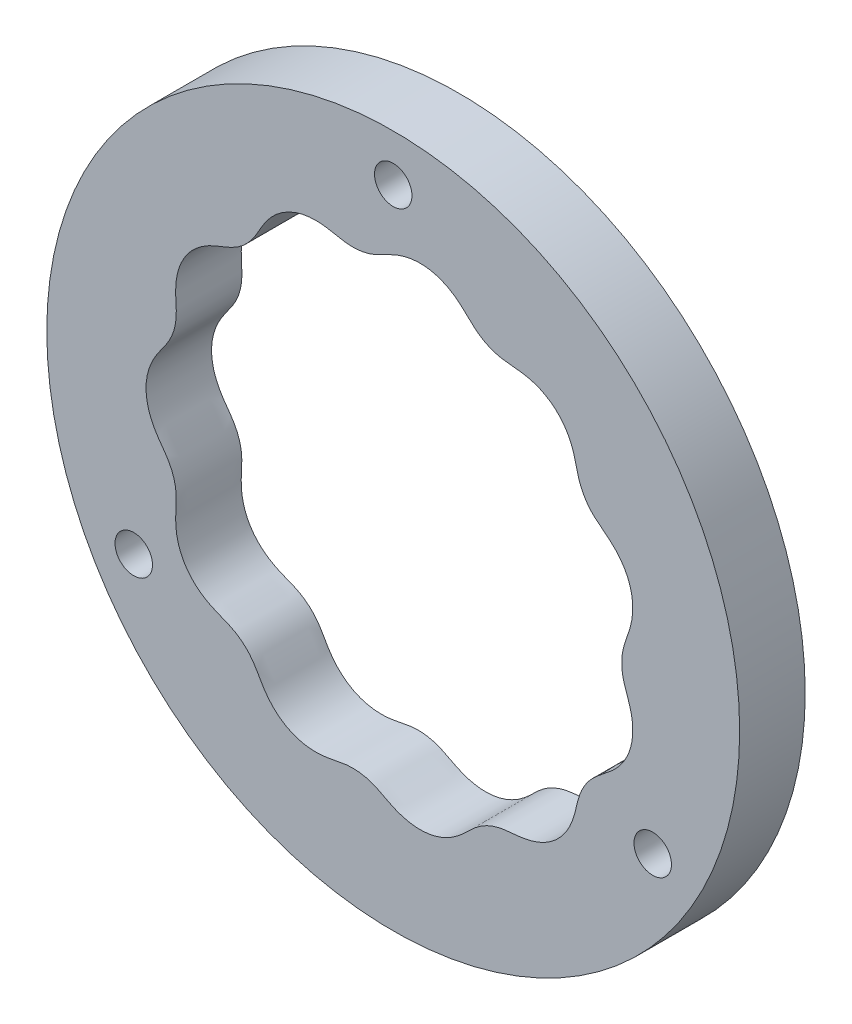
SolidWorks part; units mm, degrees
ref_plane "Front Plane" through (0, 0, 0) normal (0, 0, 1) x (1, 0, 0)
ref_plane "Top Plane" through (0, 0, 0) normal (0, 1, 0) x (1, 0, 0)
ref_plane "Right Plane" through (0, 0, 0) normal (1, 0, 0) x (0, 0, -1)
curve "Curve1"
sketch "Sketch2" plane through (0, 0, 0) normal (0, 0, 1) x (1, 0, 0)
  circle A0 centre (0, 0) radius 37
  dimension "D1" = 74
extrude "Boss-Extrude1" add sketch "Sketch2" along normal blind 7
sketch "Sketch3" plane through (0, 0, 0) normal (0, 0, 1) x (1, 0, 0)
  spline S3 degree 3 poles (-23.4157, -6.8604) (-23.2888, -7.2958) (-23.217, -7.7095) (-23.1554, -8.5437) (-23.1678, -8.9644) (-23.2129, -9.8075) (-23.2391, -10.2294) (-23.2305, -11.0671) (-23.1977, -11.483) (-23.0906, -12.1011) (-23.0455, -12.3062) (-22.9347, -12.7142) (-22.8684, -12.9184) (-22.6392, -13.5189) (-22.4484, -13.8979) (-21.9918, -14.6135) (-21.7225, -14.953) (-21.1289, -15.5624) (-20.8039, -15.8351) (-20.2767, -16.199) (-20.0939, -16.313) (-19.7217, -16.5237) (-19.5317, -16.6209) (-18.952, -16.8927) (-18.5518, -17.0457) (-17.7553, -17.3595) (-17.3623, -17.5264) (-16.8043, -17.8374) (-16.6231, -17.9504) (-16.2718, -18.1975) (-16.1007, -18.3324) (-15.618, -18.7579) (-15.3336, -19.0723) (-14.8288, -19.7538) (-14.6109, -20.1231) (-14.1864, -20.8702) (-13.975, -21.2444) (-13.4977, -21.9545) (-13.2338, -22.2918) (-12.7859, -22.7614) (-12.6283, -22.9117) (-12.302, -23.1928) (-12.1327, -23.3247) (-11.7815, -23.5705) (-11.5997, -23.6846) (-11.223, -23.8944) (-11.0271, -23.9906) (-10.431, -24.2455) (-10.0214, -24.3721) (-9.1786, -24.5422) (-8.7425, -24.5847) (-7.8842, -24.5884) (-7.4577, -24.5502) (-6.6084, -24.4197) (-6.1857, -24.3257) (-5.3382, -24.1656) (-4.9129, -24.106) (-4.2692, -24.0882) (-4.0538, -24.0934) (-3.6209, -24.1282) (-3.4023, -24.158) (-2.7639, -24.2822) (-2.3556, -24.4114) (-1.5664, -24.7426) (-1.1862, -24.9468) (-0.4226, -25.3465) (-0.0378, -25.5379) (0.7548, -25.8527) (1.1619, -25.9783) (1.793, -26.1069) (2.008, -26.14) (2.4388, -26.1839) (2.6538, -26.1948) (3.2973, -26.1948) (3.7245, -26.1511) (4.5751, -25.9728) (4.9846, -25.8407) (5.7713, -25.4979) (6.1516, -25.2844) (6.8648, -24.7948) (7.1976, -24.5181) (7.8356, -23.929) (8.1406, -23.6171) (8.7833, -23.0338) (9.1235, -22.7657) (9.6815, -22.4226) (9.8766, -22.3167) (10.2748, -22.1294) (10.4766, -22.0481) (11.0899, -21.839) (11.5096, -21.7477) (12.3636, -21.6309) (12.7977, -21.604) (13.6582, -21.5168) (14.0835, -21.455) (14.9137, -21.2583) (15.3191, -21.125) (15.91, -20.8627) (16.1053, -20.7641) (16.4824, -20.5485) (16.6641, -20.4318) (17.1889, -20.0554) (17.5124, -19.7689) (18.1012, -19.1251) (18.3574, -18.778) (18.7992, -18.0377) (18.9853, -17.6408) (19.2859, -16.8269) (19.4, -16.4083) (19.6028, -15.563) (19.6945, -15.137) (19.951, -14.3104) (20.1151, -13.9094) (20.54, -13.1409) (20.7925, -12.7863) (21.3634, -12.1428) (21.6847, -11.8535) (22.3639, -11.3082) (22.717, -11.0488) (23.3843, -10.4896) (23.7001, -10.1909) (24.2747, -9.5327) (24.5347, -9.1717) (24.9684, -8.4153) (25.146, -8.0168) (25.4173, -7.1766) (25.5064, -6.7484) (25.5734, -6.0983) (25.5846, -5.8801) (25.5847, -5.4406) (25.5735, -5.2195) (25.5087, -4.5665) (25.4235, -4.14) (25.1911, -3.3) (25.0414, -2.887) (24.7498, -2.0595) (24.6146, -1.6433) (24.482, -1.0027) (24.4488, -0.7866) (24.4063, -0.3489) (24.3972, -0.1253) (24.408, 0.5376) (24.4656, 0.9688) (24.664, 1.8132) (24.8077, 2.2258) (25.1001, 3.05) (25.243, 3.4629) (25.4582, 4.3015) (25.533, 4.7269) (25.5985, 5.5932) (25.5886, 6.038) (25.4778, 6.9019) (25.3784, 7.3255) (25.1607, 7.9479) (25.0769, 8.1519) (24.8904, 8.5464) (24.7873, 8.738) (24.562, 9.1102) (24.4399, 9.2907) (24.1768, 9.6411) (24.0357, 9.8111) (23.5925, 10.2978) (23.268, 10.5931) (22.586, 11.1497) (22.2283, 11.4104) (21.5501, 11.9712) (21.232, 12.2737) (20.8084, 12.7843) (20.6749, 12.9645) (20.4296, 13.3395) (20.3194, 13.5316) (20.0231, 14.1204) (19.8735, 14.5305) (19.6375, 15.3741) (19.5486, 15.8065) (19.3329, 16.6575) (19.2054, 17.0749) (18.8768, 17.8792) (18.6765, 18.2679) (18.1942, 19.0051) (17.9196, 19.3434) (17.3031, 19.959) (16.9569, 20.2386) (16.224, 20.7129) (15.8359, 20.9101) (15.2226, 21.1486) (15.0127, 21.2185) (14.591, 21.3375) (14.3782, 21.3871) (13.7348, 21.5104) (13.2988, 21.5562) (12.4238, 21.6332) (11.986, 21.67) (11.1272, 21.8307) (10.7037, 21.953) (9.8856, 22.2979) (9.5059, 22.5127) (8.7982, 23.0166) (8.472, 23.3085) (7.8374, 23.9178) (7.5246, 24.2284) (6.8586, 24.7973) (6.5067, 25.0574) (5.9392, 25.3961) (5.7423, 25.5011) (5.3409, 25.6895) (5.1368, 25.7727) (4.5143, 25.9898) (4.0847, 26.0914) (3.2014, 26.2018) (2.7616, 26.2092) (1.8852, 26.1336) (1.4445, 26.0486) (0.5991, 25.8006) (0.1919, 25.6373) (-0.6023, 25.2598) (-0.989, 25.0443) (-1.7756, 24.6483) (-2.1778, 24.4736) (-3.018, 24.2189) (-3.4609, 24.1368) (-4.3363, 24.0756) (-4.7726, 24.0958) (-5.6431, 24.213) (-6.0769, 24.3101) (-6.9459, 24.4771) (-7.3821, 24.5446) (-8.0427, 24.5858) (-8.2639, 24.5901) (-8.7086, 24.5772) (-8.9329, 24.5597) (-9.5944, 24.4738) (-10.0245, 24.3725) (-10.6529, 24.1517) (-10.8608, 24.0659) (-11.2633, 23.8739) (-11.4579, 23.7678) (-12.0226, 23.4202) (-12.3748, 23.1485) (-13.0235, 22.5326) (-13.311, 22.1968) (-13.8281, 21.4811) (-14.0558, 21.1) (-14.4959, 20.3261) (-14.7127, 19.9369) (-15.2185, 19.2111) (-15.5059, 18.8735) (-16.0017, 18.4146) (-16.176, 18.2713) (-16.5345, 18.0089) (-16.7198, 17.8888) (-17.2924, 17.5588) (-17.6982, 17.383) (-18.5234, 17.056) (-18.9395, 16.8986) (-19.737, 16.5246) (-20.1197, 16.31) (-20.6608, 15.9324) (-20.8359, 15.7974) (-21.1742, 15.5073) (-21.3367, 15.3527) (-21.7936, 14.8698) (-22.0619, 14.5191) (-22.4083, 13.9488) (-22.5146, 13.7506) (-22.7033, 13.3485) (-22.7865, 13.1436) (-22.9313, 12.7263) (-22.9929, 12.514) (-23.0951, 12.0819) (-23.1357, 11.8613) (-23.2255, 11.1982) (-23.2424, 10.7533) (-23.2228, 9.8599) (-23.1854, 9.412) (-23.1582, 8.5183) (-23.174, 8.0726) (-23.2775, 7.4074) (-23.3249, 7.1852) (-23.4462, 6.7463) (-23.5188, 6.5334) (-23.7695, 5.9129) (-23.9831, 5.5247) (-24.4718, 4.7821) (-24.7449, 4.4266) (-25.2541, 3.6953) (-25.4892, 3.3198) (-25.8856, 2.5317) (-26.0491, 2.1177) (-26.2883, 1.2565) (-26.3616, 0.8203) (-26.4154, -0.0635) (-26.3943, -0.5152) (-26.2594, -1.3907) (-26.1464, -1.8184) (-25.8328, -2.6547) (-25.6344, -3.0549) (-25.1785, -3.8163) (-24.9185, -4.1786) (-24.3951, -4.9014) (-24.1385, -5.2657) (-23.8169, -5.8469) (-23.7197, -6.0462) (-23.5901, -6.3541) (-23.5497, -6.4583) (-23.4934, -6.6169) (-23.4753, -6.6702) (-23.4493, -6.7507) (-23.4408, -6.7776) (-23.4242, -6.8317) (-23.4157, -6.8604) (-23.2888, -7.2958) (-23.217, -7.7095) knots -0.000488 -0.000488 0 0 0.007813 0.007813 0.015625 0.015625 0.023438 0.023438 0.03125 0.03125 0.035156 0.035156 0.039063 0.039063 0.046875 0.046875 0.054688 0.054688 0.0625 0.0625 0.066406 0.066406 0.070313 0.070313 0.078125 0.078125 0.085938 0.085938 0.089844 0.089844 0.09375 0.09375 0.101563 0.101563 0.109375 0.109375 0.117188 0.117188 0.125 0.125 0.128906 0.128906 0.132813 0.132813 0.136719 0.136719 0.140625 0.140625 0.148438 0.148438 0.15625 0.15625 0.164063 0.164063 0.171875 0.171875 0.179688 0.179688 0.183594 0.183594 0.1875 0.1875 0.195313 0.195313 0.203125 0.203125 0.210938 0.210938 0.21875 0.21875 0.222656 0.222656 0.226563 0.226563 0.234375 0.234375 0.242188 0.242188 0.25 0.25 0.257813 0.257813 0.265625 0.265625 0.273438 0.273438 0.277344 0.277344 0.28125 0.28125 0.289063 0.289063 0.296875 0.296875 0.304688 0.304688 0.3125 0.3125 0.316406 0.316406 0.320313 0.320313 0.328125 0.328125 0.335938 0.335938 0.34375 0.34375 0.351563 0.351563 0.359375 0.359375 0.367188 0.367188 0.375 0.375 0.382813 0.382813 0.390625 0.390625 0.398438 0.398438 0.40625 0.40625 0.414063 0.414063 0.421875 0.421875 0.425781 0.425781 0.429688 0.429688 0.4375 0.4375 0.445313 0.445313 0.453125 0.453125 0.457031 0.457031 0.460938 0.460938 0.46875 0.46875 0.476562 0.476562 0.484375 0.484375 0.492187 0.492187 0.5 0.5 0.507812 0.507812 0.511719 0.511719 0.515625 0.515625 0.519531 0.519531 0.523437 0.523437 0.53125 0.53125 0.539062 0.539062 0.546875 0.546875 0.550781 0.550781 0.554687 0.554687 0.5625 0.5625 0.570312 0.570312 0.578125 0.578125 0.585937 0.585937 0.59375 0.59375 0.601562 0.601562 0.609375 0.609375 0.613281 0.613281 0.617187 0.617187 0.625 0.625 0.632812 0.632812 0.640625 0.640625 0.648437 0.648437 0.65625 0.65625 0.664062 0.664062 0.671875 0.671875 0.675781 0.675781 0.679687 0.679687 0.6875 0.6875 0.695312 0.695312 0.703125 0.703125 0.710937 0.710937 0.71875 0.71875 0.726562 0.726562 0.734375 0.734375 0.742187 0.742187 0.75 0.75 0.757812 0.757812 0.761719 0.761719 0.765625 0.765625 0.773437 0.773437 0.777344 0.777344 0.78125 0.78125 0.789062 0.789062 0.796875 0.796875 0.804687 0.804687 0.8125 0.8125 0.820312 0.820312 0.824219 0.824219 0.828125 0.828125 0.835937 0.835937 0.84375 0.84375 0.851562 0.851562 0.855469 0.855469 0.859375 0.859375 0.867187 0.867187 0.871094 0.871094 0.875 0.875 0.878906 0.878906 0.882812 0.882812 0.890625 0.890625 0.898437 0.898437 0.90625 0.90625 0.910156 0.910156 0.914062 0.914062 0.921875 0.921875 0.929687 0.929687 0.9375 0.9375 0.945312 0.945312 0.953125 0.953125 0.960937 0.960937 0.96875 0.96875 0.976562 0.976562 0.984375 0.984375 0.992188 0.992188 0.996094 0.996094 0.998047 0.998047 0.999023 0.999023 0.999512 0.999512 1 1 1.007813 1.007813 1.015625 only from (-23.4082, -6.886) to (-23.4082, -6.886)
  spline S4 degree 3 poles (-23.4157, -6.8604) (-23.2888, -7.2958) (-23.217, -7.7095) (-23.1554, -8.5437) (-23.1678, -8.9644) (-23.2129, -9.8075) (-23.2391, -10.2294) (-23.2305, -11.0671) (-23.1977, -11.483) (-23.0906, -12.1011) (-23.0455, -12.3062) (-22.9347, -12.7142) (-22.8684, -12.9184) (-22.6392, -13.5189) (-22.4484, -13.8979) (-21.9918, -14.6135) (-21.7225, -14.953) (-21.1289, -15.5624) (-20.8039, -15.8351) (-20.2767, -16.199) (-20.0939, -16.313) (-19.7217, -16.5237) (-19.5317, -16.6209) (-18.952, -16.8927) (-18.5518, -17.0457) (-17.7553, -17.3595) (-17.3623, -17.5264) (-16.8043, -17.8374) (-16.6231, -17.9504) (-16.2718, -18.1975) (-16.1007, -18.3324) (-15.618, -18.7579) (-15.3336, -19.0723) (-14.8288, -19.7538) (-14.6109, -20.1231) (-14.1864, -20.8702) (-13.975, -21.2444) (-13.4977, -21.9545) (-13.2338, -22.2918) (-12.7859, -22.7614) (-12.6283, -22.9117) (-12.302, -23.1928) (-12.1327, -23.3247) (-11.7815, -23.5705) (-11.5997, -23.6846) (-11.223, -23.8944) (-11.0271, -23.9906) (-10.431, -24.2455) (-10.0214, -24.3721) (-9.1786, -24.5422) (-8.7425, -24.5847) (-7.8842, -24.5884) (-7.4577, -24.5502) (-6.6084, -24.4197) (-6.1857, -24.3257) (-5.3382, -24.1656) (-4.9129, -24.106) (-4.2692, -24.0882) (-4.0538, -24.0934) (-3.6209, -24.1282) (-3.4023, -24.158) (-2.7639, -24.2822) (-2.3556, -24.4114) (-1.5664, -24.7426) (-1.1862, -24.9468) (-0.4226, -25.3465) (-0.0378, -25.5379) (0.7548, -25.8527) (1.1619, -25.9783) (1.793, -26.1069) (2.008, -26.14) (2.4388, -26.1839) (2.6538, -26.1948) (3.2973, -26.1948) (3.7245, -26.1511) (4.5751, -25.9728) (4.9846, -25.8407) (5.7713, -25.4979) (6.1516, -25.2844) (6.8648, -24.7948) (7.1976, -24.5181) (7.8356, -23.929) (8.1406, -23.6171) (8.7833, -23.0338) (9.1235, -22.7657) (9.6815, -22.4226) (9.8766, -22.3167) (10.2748, -22.1294) (10.4766, -22.0481) (11.0899, -21.839) (11.5096, -21.7477) (12.3636, -21.6309) (12.7977, -21.604) (13.6582, -21.5168) (14.0835, -21.455) (14.9137, -21.2583) (15.3191, -21.125) (15.91, -20.8627) (16.1053, -20.7641) (16.4824, -20.5485) (16.6641, -20.4318) (17.1889, -20.0554) (17.5124, -19.7689) (18.1012, -19.1251) (18.3574, -18.778) (18.7992, -18.0377) (18.9853, -17.6408) (19.2859, -16.8269) (19.4, -16.4083) (19.6028, -15.563) (19.6945, -15.137) (19.951, -14.3104) (20.1151, -13.9094) (20.54, -13.1409) (20.7925, -12.7863) (21.3634, -12.1428) (21.6847, -11.8535) (22.3639, -11.3082) (22.717, -11.0488) (23.3843, -10.4896) (23.7001, -10.1909) (24.2747, -9.5327) (24.5347, -9.1717) (24.9684, -8.4153) (25.146, -8.0168) (25.4173, -7.1766) (25.5064, -6.7484) (25.5734, -6.0983) (25.5846, -5.8801) (25.5847, -5.4406) (25.5735, -5.2195) (25.5087, -4.5665) (25.4235, -4.14) (25.1911, -3.3) (25.0414, -2.887) (24.7498, -2.0595) (24.6146, -1.6433) (24.482, -1.0027) (24.4488, -0.7866) (24.4063, -0.3489) (24.3972, -0.1253) (24.408, 0.5376) (24.4656, 0.9688) (24.664, 1.8132) (24.8077, 2.2258) (25.1001, 3.05) (25.243, 3.4629) (25.4582, 4.3015) (25.533, 4.7269) (25.5985, 5.5932) (25.5886, 6.038) (25.4778, 6.9019) (25.3784, 7.3255) (25.1607, 7.9479) (25.0769, 8.1519) (24.8904, 8.5464) (24.7873, 8.738) (24.562, 9.1102) (24.4399, 9.2907) (24.1768, 9.6411) (24.0357, 9.8111) (23.5925, 10.2978) (23.268, 10.5931) (22.586, 11.1497) (22.2283, 11.4104) (21.5501, 11.9712) (21.232, 12.2737) (20.8084, 12.7843) (20.6749, 12.9645) (20.4296, 13.3395) (20.3194, 13.5316) (20.0231, 14.1204) (19.8735, 14.5305) (19.6375, 15.3741) (19.5486, 15.8065) (19.3329, 16.6575) (19.2054, 17.0749) (18.8768, 17.8792) (18.6765, 18.2679) (18.1942, 19.0051) (17.9196, 19.3434) (17.3031, 19.959) (16.9569, 20.2386) (16.224, 20.7129) (15.8359, 20.9101) (15.2226, 21.1486) (15.0127, 21.2185) (14.591, 21.3375) (14.3782, 21.3871) (13.7348, 21.5104) (13.2988, 21.5562) (12.4238, 21.6332) (11.986, 21.67) (11.1272, 21.8307) (10.7037, 21.953) (9.8856, 22.2979) (9.5059, 22.5127) (8.7982, 23.0166) (8.472, 23.3085) (7.8374, 23.9178) (7.5246, 24.2284) (6.8586, 24.7973) (6.5067, 25.0574) (5.9392, 25.3961) (5.7423, 25.5011) (5.3409, 25.6895) (5.1368, 25.7727) (4.5143, 25.9898) (4.0847, 26.0914) (3.2014, 26.2018) (2.7616, 26.2092) (1.8852, 26.1336) (1.4445, 26.0486) (0.5991, 25.8006) (0.1919, 25.6373) (-0.6023, 25.2598) (-0.989, 25.0443) (-1.7756, 24.6483) (-2.1778, 24.4736) (-3.018, 24.2189) (-3.4609, 24.1368) (-4.3363, 24.0756) (-4.7726, 24.0958) (-5.6431, 24.213) (-6.0769, 24.3101) (-6.9459, 24.4771) (-7.3821, 24.5446) (-8.0427, 24.5858) (-8.2639, 24.5901) (-8.7086, 24.5772) (-8.9329, 24.5597) (-9.5944, 24.4738) (-10.0245, 24.3725) (-10.6529, 24.1517) (-10.8608, 24.0659) (-11.2633, 23.8739) (-11.4579, 23.7678) (-12.0226, 23.4202) (-12.3748, 23.1485) (-13.0235, 22.5326) (-13.311, 22.1968) (-13.8281, 21.4811) (-14.0558, 21.1) (-14.4959, 20.3261) (-14.7127, 19.9369) (-15.2185, 19.2111) (-15.5059, 18.8735) (-16.0017, 18.4146) (-16.176, 18.2713) (-16.5345, 18.0089) (-16.7198, 17.8888) (-17.2924, 17.5588) (-17.6982, 17.383) (-18.5234, 17.056) (-18.9395, 16.8986) (-19.737, 16.5246) (-20.1197, 16.31) (-20.6608, 15.9324) (-20.8359, 15.7974) (-21.1742, 15.5073) (-21.3367, 15.3527) (-21.7936, 14.8698) (-22.0619, 14.5191) (-22.4083, 13.9488) (-22.5146, 13.7506) (-22.7033, 13.3485) (-22.7865, 13.1436) (-22.9313, 12.7263) (-22.9929, 12.514) (-23.0951, 12.0819) (-23.1357, 11.8613) (-23.2255, 11.1982) (-23.2424, 10.7533) (-23.2228, 9.8599) (-23.1854, 9.412) (-23.1582, 8.5183) (-23.174, 8.0726) (-23.2775, 7.4074) (-23.3249, 7.1852) (-23.4462, 6.7463) (-23.5188, 6.5334) (-23.7695, 5.9129) (-23.9831, 5.5247) (-24.4718, 4.7821) (-24.7449, 4.4266) (-25.2541, 3.6953) (-25.4892, 3.3198) (-25.8856, 2.5317) (-26.0491, 2.1177) (-26.2883, 1.2565) (-26.3616, 0.8203) (-26.4154, -0.0635) (-26.3943, -0.5152) (-26.2594, -1.3907) (-26.1464, -1.8184) (-25.8328, -2.6547) (-25.6344, -3.0549) (-25.1785, -3.8163) (-24.9185, -4.1786) (-24.3951, -4.9014) (-24.1385, -5.2657) (-23.8169, -5.8469) (-23.7197, -6.0462) (-23.5901, -6.3541) (-23.5497, -6.4583) (-23.4934, -6.6169) (-23.4753, -6.6702) (-23.4493, -6.7507) (-23.4408, -6.7776) (-23.4242, -6.8317) (-23.4157, -6.8604) (-23.2888, -7.2958) (-23.217, -7.7095) knots -0.000488 -0.000488 0 0 0.007813 0.007813 0.015625 0.015625 0.023438 0.023438 0.03125 0.03125 0.035156 0.035156 0.039063 0.039063 0.046875 0.046875 0.054688 0.054688 0.0625 0.0625 0.066406 0.066406 0.070313 0.070313 0.078125 0.078125 0.085938 0.085938 0.089844 0.089844 0.09375 0.09375 0.101563 0.101563 0.109375 0.109375 0.117188 0.117188 0.125 0.125 0.128906 0.128906 0.132813 0.132813 0.136719 0.136719 0.140625 0.140625 0.148438 0.148438 0.15625 0.15625 0.164063 0.164063 0.171875 0.171875 0.179688 0.179688 0.183594 0.183594 0.1875 0.1875 0.195313 0.195313 0.203125 0.203125 0.210938 0.210938 0.21875 0.21875 0.222656 0.222656 0.226563 0.226563 0.234375 0.234375 0.242188 0.242188 0.25 0.25 0.257813 0.257813 0.265625 0.265625 0.273438 0.273438 0.277344 0.277344 0.28125 0.28125 0.289063 0.289063 0.296875 0.296875 0.304688 0.304688 0.3125 0.3125 0.316406 0.316406 0.320313 0.320313 0.328125 0.328125 0.335938 0.335938 0.34375 0.34375 0.351563 0.351563 0.359375 0.359375 0.367188 0.367188 0.375 0.375 0.382813 0.382813 0.390625 0.390625 0.398438 0.398438 0.40625 0.40625 0.414063 0.414063 0.421875 0.421875 0.425781 0.425781 0.429688 0.429688 0.4375 0.4375 0.445313 0.445313 0.453125 0.453125 0.457031 0.457031 0.460938 0.460938 0.46875 0.46875 0.476562 0.476562 0.484375 0.484375 0.492187 0.492187 0.5 0.5 0.507812 0.507812 0.511719 0.511719 0.515625 0.515625 0.519531 0.519531 0.523437 0.523437 0.53125 0.53125 0.539062 0.539062 0.546875 0.546875 0.550781 0.550781 0.554687 0.554687 0.5625 0.5625 0.570312 0.570312 0.578125 0.578125 0.585937 0.585937 0.59375 0.59375 0.601562 0.601562 0.609375 0.609375 0.613281 0.613281 0.617187 0.617187 0.625 0.625 0.632812 0.632812 0.640625 0.640625 0.648437 0.648437 0.65625 0.65625 0.664062 0.664062 0.671875 0.671875 0.675781 0.675781 0.679687 0.679687 0.6875 0.6875 0.695312 0.695312 0.703125 0.703125 0.710937 0.710937 0.71875 0.71875 0.726562 0.726562 0.734375 0.734375 0.742187 0.742187 0.75 0.75 0.757812 0.757812 0.761719 0.761719 0.765625 0.765625 0.773437 0.773437 0.777344 0.777344 0.78125 0.78125 0.789062 0.789062 0.796875 0.796875 0.804687 0.804687 0.8125 0.8125 0.820312 0.820312 0.824219 0.824219 0.828125 0.828125 0.835937 0.835937 0.84375 0.84375 0.851562 0.851562 0.855469 0.855469 0.859375 0.859375 0.867187 0.867187 0.871094 0.871094 0.875 0.875 0.878906 0.878906 0.882812 0.882812 0.890625 0.890625 0.898437 0.898437 0.90625 0.90625 0.910156 0.910156 0.914062 0.914062 0.921875 0.921875 0.929687 0.929687 0.9375 0.9375 0.945312 0.945312 0.953125 0.953125 0.960937 0.960937 0.96875 0.96875 0.976562 0.976562 0.984375 0.984375 0.992188 0.992188 0.996094 0.996094 0.998047 0.998047 0.999023 0.999023 0.999512 0.999512 1 1 1.007813 1.007813 1.015625 only from (-23.4082, -6.886) to (-23.4082, -6.886)
  dimension "D1" = 0.4
extrude "Cut-Extrude1" cut sketch "Sketch3" along normal through all
sketch "Sketch4" plane through (0, 0, 0) normal (0, 0, 1) x (1, 0, 0)
  circle A0 centre (0, 32) radius 2
  point P2 (0, 0)
  dimension "D1" = 32
  dimension "D2" = 4
extrude "Cut-Extrude3" cut sketch "Sketch4" along normal through all
pattern_circular "CirPattern1" count 3 over 360 about axis through (0, 0, 0) along (0, 0, 1) of "Cut-Extrude3"
